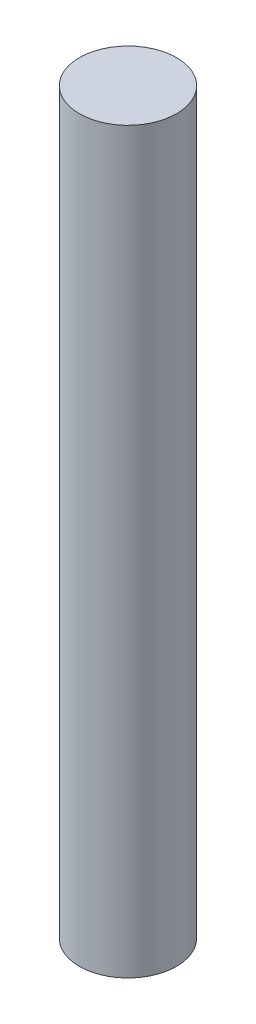
SolidWorks part; units mm, degrees
ref_plane "Front Plane" through (0, 0, 0) normal (0, 0, 1) x (1, 0, 0)
ref_plane "Top Plane" through (0, 0, 0) normal (0, 1, 0) x (1, 0, 0)
ref_plane "Right Plane" through (0, 0, 0) normal (1, 0, 0) x (0, 0, -1)
sketch "Sketch1" plane through (0, 0, 0) normal (0, 1, 0) x (1, 0, 0)
  circle A0 centre (0, 0) radius 2.5
  dimension "D1" = 5
extrude "Boss-Extrude1" add sketch "Sketch1" along normal blind 38
